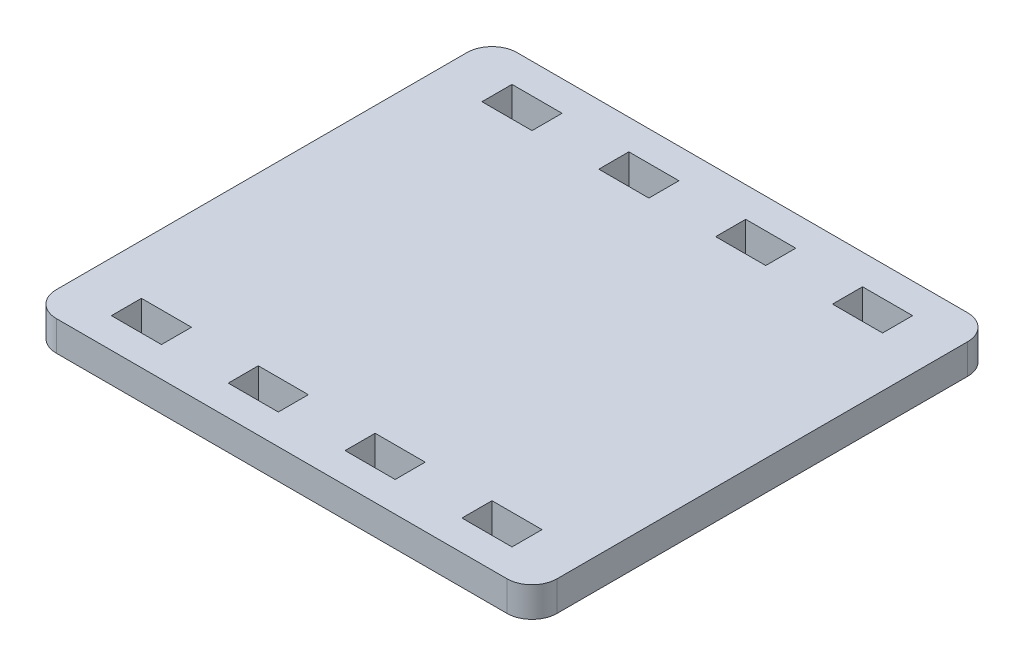
SolidWorks part; units mm, degrees
material "Maple"
ref_plane "Front Plane" through (0, 0, 0) normal (0, 0, 1) x (1, 0, 0)
ref_plane "Top Plane" through (0, 0, 0) normal (0, 1, 0) x (1, 0, 0)
ref_plane "Right Plane" through (0, 0, 0) normal (1, 0, 0) x (0, 0, -1)
sketch "Sketch1" plane through (0, 0, 0) normal (0, 1, 0) x (1, 0, 0)
  line L0 (135, 92) -> (5, 92) construction
  line L1 (0, 0) -> (100, 0)
  line L2 (0, 0) -> (0, 92)
  line L3 (0, 92) -> (100, 92)
  line L4 (100, 0) -> (100, 92)
  line L5 (100, 12) -> (100, 80) construction
extrude "Boss-Extrude1" add sketch "Sketch1" along normal blind 6
ref_plane "Plane1" through (0, 3, 0) normal (0, 1, 0) x (1, 0, 0)
ref_plane "Plane2" through (0, 0, -46) normal (0, 0, -1) x (-1, 0, 0)
sketch "Sketch2" plane through (0, 0, 0) normal (0, -1, 0) x (1, 0, 0)
  line L0 (100, -83) -> (0, -83) construction
  line L1 (100, 0) -> (100, -92) construction
  line L2 (0, -92) -> (0, 0) construction
  line L3 (-25.85, -83) -> (25.85, -83) construction
  line L4 (85, -83) -> (61.6667, -83) construction
  point P8 (85, -83)
  point P9 (15, -83)
  point P10 (61.6667, -83)
  point P11 (38.3333, -83)
  dimension "D2" = 15
  dimension "D3" = 15
  dimension "D1" = 4
sketch "Sketch6" plane through (84.2322, 3, -39) normal (0, -1, 0) x (1, 0, 0)
  line L1 (-4.2322, -41) -> (5.7678, -41)
  line L2 (-4.2322, -41) -> (-4.2322, -47)
  line L3 (-4.2322, -47) -> (5.7678, -47)
  line L4 (5.7678, -41) -> (5.7678, -47)
  line L5 (-4.2322, -41) -> (5.7678, -47) construction
  line L6 (-4.2322, -47) -> (5.7678, -41) construction
  point P0 (0.7678, -44)
  dimension "D1" = 10
  dimension "D2" = 6
extrude "Cut-Extrude1" cut sketch "Sketch6" against normal through all and the other way through all
other "Smart-Feature1<virtual_pin-10>"
sketch "Sketch61" plane through (60.8989, 3, -39) normal (0, -1, 0) x (1, 0, 0)
  line L1 (-4.2322, -41) -> (5.7678, -41)
  line L2 (-4.2322, -41) -> (-4.2322, -47)
  line L3 (-4.2322, -47) -> (5.7678, -47)
  line L4 (5.7678, -41) -> (5.7678, -47)
  line L5 (-4.2322, -41) -> (5.7678, -47) construction
  line L6 (-4.2322, -47) -> (5.7678, -41) construction
  point P0 (0.7678, -44)
  dimension "D1" = 10
  dimension "D2" = 6
extrude "Cut-Extrude11" cut sketch "Sketch61" against normal through all and the other way through all
other "Smart-Feature2<virtual_pin-11>"
sketch "Sketch62" plane through (37.5656, 3, -39) normal (0, -1, 0) x (1, 0, 0)
  line L1 (-4.2322, -41) -> (5.7678, -41)
  line L2 (-4.2322, -41) -> (-4.2322, -47)
  line L3 (-4.2322, -47) -> (5.7678, -47)
  line L4 (5.7678, -41) -> (5.7678, -47)
  line L5 (-4.2322, -41) -> (5.7678, -47) construction
  line L6 (-4.2322, -47) -> (5.7678, -41) construction
  point P0 (0.7678, -44)
  dimension "D1" = 10
  dimension "D2" = 6
extrude "Cut-Extrude12" cut sketch "Sketch62" against normal through all and the other way through all
other "Smart-Feature3<virtual_pin-12>"
sketch "Sketch63" plane through (14.2322, 3, -39) normal (0, -1, 0) x (1, 0, 0)
  line L1 (-4.2322, -41) -> (5.7678, -41)
  line L2 (-4.2322, -41) -> (-4.2322, -47)
  line L3 (-4.2322, -47) -> (5.7678, -47)
  line L4 (5.7678, -41) -> (5.7678, -47)
  line L5 (-4.2322, -41) -> (5.7678, -47) construction
  line L6 (-4.2322, -47) -> (5.7678, -41) construction
  point P0 (0.7678, -44)
  dimension "D1" = 10
  dimension "D2" = 6
extrude "Cut-Extrude13" cut sketch "Sketch63" against normal through all and the other way through all
other "Smart-Feature4<virtual_pin-13>"
mirror "Mirror1" about plane through (0, 0, -46) normal (0, 0, -1) of "Cut-Extrude13", "Cut-Extrude12", "Cut-Extrude11", "Cut-Extrude1"
fillet "Fillet1" radius 5 4 edges at (0, 3, -92) (100, 3, 0) (0, 3, 0) (100, 3, -92)
